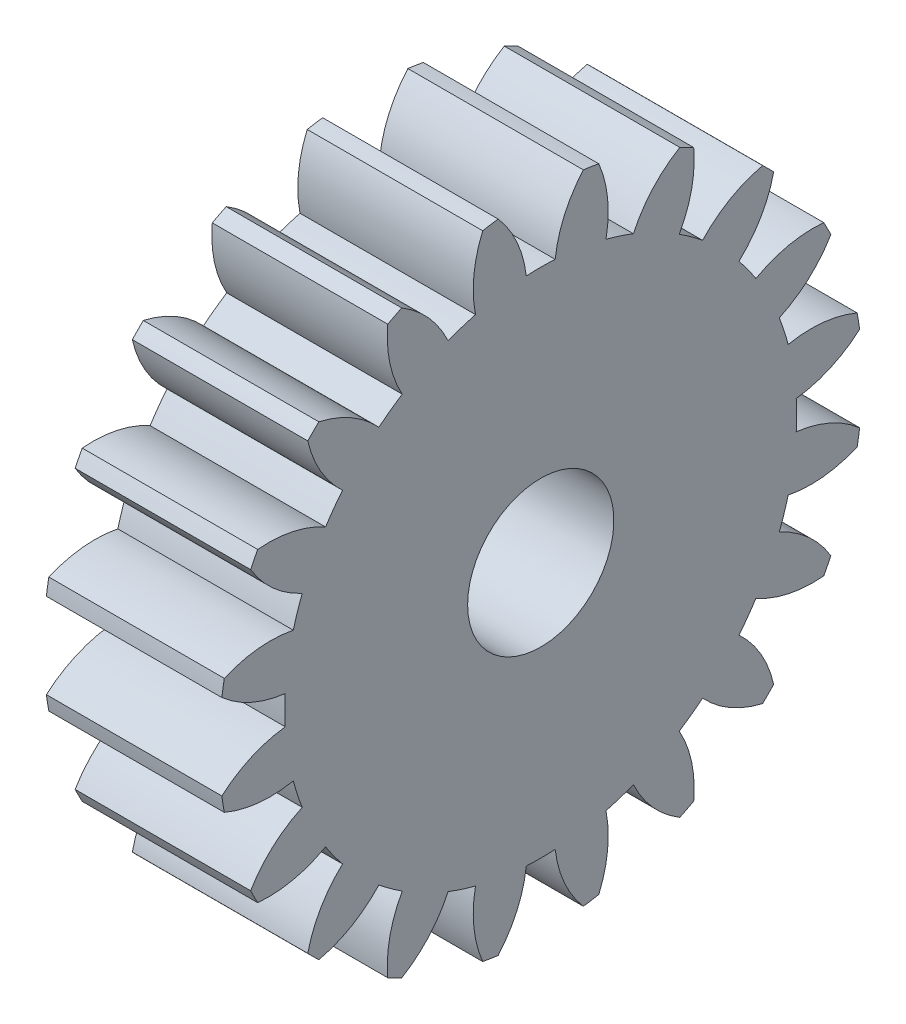
SolidWorks part; units mm, degrees
ref_plane "Plane1" through (0, 0, 0) normal (0, 0, 1) x (1, 0, 0)
ref_plane "Plane2" through (0, 0, 0) normal (0, 1, 0) x (1, 0, 0)
ref_plane "Plane3" through (0, 0, 0) normal (1, 0, 0) x (0, 0, -1)
sketch "HoldingSke" plane through (0, 0, 0) normal (0, 1, 0) x (1, 0, 0)
  line L0 (0, 0) -> (0.4698, -0.171)
  line L1 (-15, 0) -> (100, 0) construction
  line L2 (0, 0) -> (-2.1039, 2.3779)
  line L3 (0, 0) -> (-11.863, 4.5341)
  line L4 (0, 0) -> (8.1152, 2.9537)
  line L5 (0, 0) -> (-46.8476, -17.4728)
  line L6 (0, 0) -> (-9.9476, -6.7116)
  line L7 (-2.1039, 2.3779) -> (8.6586, 51.2059)
  line L8 (-76.2, 54.61) -> (-74.4, 54.61)
  line L9 (-71.009, 38.7566) -> (-53.1078, 45.2721)
  line L10 (-76.2, 71.12) -> (104.1128, 71.12)
  line L11 (0, 0) -> (-12, 0)
  line L12 (-76.2, 101.6) -> (-76.133, 101.6)
  line L13 (24.9733, 27.94) -> (52.9518, 28.4284)
  line L14 (24.9733, 27.94) -> (24.9743, 27.94)
  line L15 (24.9733, 27.94) -> (100.4006, 29.5858)
  line L16 (-63.627, -2) -> (-12.827, -2)
  circle A0 centre (0, 0) radius 5
  circle A1 centre (0, 0) radius 17.499
  circle A2 centre (0, 0) radius 37.5
  circle A3 centre (0, 0) radius 5
  dimension "MHD" = 34.998
  dimension "Hub_dia" = 75
  dimension "Bore" = 10
  dimension "MBD" = 10
  dimension "Num_teeth" = 20
  dimension "Pitch" = 0.5
  dimension "Overall_len" = 50
  dimension "Show_teeth" = 20
  dimension "Thickness" = 12
  dimension "OAL" = 50.0001
  dimension "T_dim" = 1.8
  dimension "Ap" = 20
  dimension "H" = 19.05
  dimension "Pitch_radius" = 180.3128
  dimension "Width" = 12
  dimension "Backlash" = 0.067
  dimension "Addendum_fac" = 1
  dimension "Dedendum_fac" = 1.25
  dimension "Clearance_fac" = 0.25
  dimension "Dedendum_add" = 0.001
  dimension "Module" = 2
sketch "BasProSke" plane through (0, 0, 0) normal (0, 1, 0) x (1, 0, 0)
  line L0 (-10, 0) -> (60, 0) construction
  line L1 (0, 0) -> (0, 22)
  line L2 (0, 0) -> (12, 0)
  line L3 (12, 0) -> (12, 22)
  line L4 (12, 22) -> (0, 22)
  dimension "Thickness" = 12
  dimension "Diameter" = 44
revolve "Base-Revolve" add sketch "BasProSke" angle 360 about L0
sketch "TooCutSke" plane through (0, 0, 0) normal (1, 0, 0) x (0, 0, -1)
  line L1 (0, 0) -> (0, 107) construction
  line L2 (0, 0) -> (-1.6864, 19.9288) construction
  line L3 (0, 0) -> (-6.2409, 39.4033) construction
  line L4 (-1.6864, 19.9288) -> (-3.1204, 19.7016) construction
  arc A0 (0.9862, 17.4712) -> (-0.9862, 17.4712) centre (0, 0) ccw
  arc A1 (2.9329, 21.8293) -> (-2.9329, 21.8293) centre (0, 0) ccw
  circle A2 centre (0, 0) radius 20 construction
  circle A3 centre (0, 0) radius 18.7939 construction
  arc A4 (-0.9862, 17.4712) -> (-2.9329, 21.8293) centre (-8.9313, 16.536) ccw
  arc A5 (2.9329, 21.8293) -> (0.9862, 17.4712) centre (8.9313, 16.536) ccw
  dimension "Root_dia" = 34.998
  dimension "Overcut_dia" = 44.0508
  dimension "Pitch_dia" = 40
  dimension "Base_dia" = 37.5877
  dimension "Flank_rad" = 8
  dimension "Half_ang" = 9
  dimension "Half_CT" = 1.4519
extrude "ToothCut" cut sketch "TooCutSke" along normal through all
fillet "Breaks" [suppressed] radius 0.04
fillet "RootFillets" [suppressed] radius 0.501
pattern_circular "TeethCuts" count 20 every 18 about axis through (-10, 0, 0) along (1, 0, 0) of "ToothCut", "RootFillets", "Breaks"
sketch "HubNeaOneSke" plane through (0, 0, 0) normal (-1, 0, 0) x (0, 0, 1)
  circle A0 centre (0, 0) radius 17.499
  dimension "Diameter" = 34.998
extrude "HubNearOne" [suppressed] add sketch "HubNeaOneSke" along normal blind 38.0001
sketch "HubNeaBotSke" plane through (0, 0, 0) normal (-1, 0, 0) x (0, 0, 1)
  circle A0 centre (0, 0) radius 17.499
  dimension "Diameter" = 34.998
extrude "HubNearBoth" [suppressed] add sketch "HubNeaBotSke" along normal blind 19
ref_plane "FarPln" through (12, 0, 0) normal (1, 0, 0) x (0, 0, -1)
sketch "HubFarSke" plane through (12, 0, 0) normal (1, 0, 0) x (0, 0, -1)
  circle A0 centre (0, 0) radius 17.499
  dimension "Diameter" = 34.998
extrude "HubFar" [suppressed] add sketch "HubFarSke" along normal blind 19
sketch "BorSke" plane through (0, 0, 0) normal (1, 0, 0) x (0, 0, -1)
  circle A0 centre (0, 0) radius 5
  dimension "Diameter" = 10
extrude "Bore" cut sketch "BorSke" along normal mid plane 100.0001
sketch "KeySke" plane through (0, 0, 0) normal (1, 0, 0) x (0, 0, -1)
  line L0 (-2, 0) -> (-2, 6.8)
  line L1 (-2, 6.8) -> (2, 6.8)
  line L2 (2, 6.8) -> (2, 0)
  line L3 (0, 0) -> (0, 34) construction
  line L4 (-2, 0) -> (2, 0)
  dimension "Offset" = 6.8
  dimension "Width" = 4
extrude "Keyway" [suppressed] cut sketch "KeySke" along normal mid plane 100.0001
pattern_circular "Keyway2" [suppressed] count 2 every 90 about axis through (-10, 0, 0) along (1, 0, 0)
equation "' \"Module@HoldingSke\" = 6.35"
equation "' \"Num_teeth@HoldingSke\" = 12"
equation "' \"Ap@HoldingSke\" =  20"
equation "' \"Ap@HoldingSke\" = 20"
equation "' \"Width@HoldingSke\" = 0.5 * 25.4"
equation "' \"Hub_dia@HoldingSke\"= 1 * 25.4"
equation "' \"Hub_dia@HoldingSke\" = 1 * 25.4"
equation "' \"Overall_len@HoldingSke\" = 1.0 * 25.4"
equation "' \"Bore@HoldingSke\" = 0.75 * 25.4"
equation "' \"T_dim@HoldingSke\" = 0.1 * 25.4"
equation "' \"Width@KeySke\" = 0.25 * 25.4"
equation "' \"Show_teeth@HoldingSke\" = 13"
equation "' \"Backlash@HoldingSke\" = 0.009 * 25.4"
equation "' \"Addendum_fac@HoldingSke\" = 1.0"
equation "' \"Dedendum_fac@HoldingSke\" = 1.25"
equation "' \"Dedendum_add@HoldingSke\" = 0.00005 * 25.4"
equation "' \"Clearance_fac@HoldingSke\" = 0.25"
equation "\"Pitch@HoldingSke\" = 1 / \"Module@HoldingSke\""
equation "\"Overcut_dia@TooCutSke\" = (\"Num_teeth@HoldingSke\" + 2 * \"Addendum_fac@HoldingSke\") / \"Pitch@HoldingSke\" + 0.002 * 25.4"
equation "\"Pitch_dia@TooCutSke\" = \"Num_teeth@HoldingSke\" / \"Pitch@HoldingSke\""
equation "\"Base_dia@TooCutSke\" = \"Num_teeth@HoldingSke\" / \"Pitch@HoldingSke\" * cos((\"Ap@HoldingSke\"  * 3.14159265 / 180))"
equation "\"Root_dia@TooCutSke\" = (\"Num_teeth@HoldingSke\" + 2) / \"Pitch@HoldingSke\" - 2 * (\"Addendum_fac@HoldingSke\" + \"Dedendum_fac@HoldingSke\") / \"Pitch@HoldingSke\" - \"Dedendum_add@HoldingSke\" * 2"
equation "\"Half_ang@TooCutSke\" = 180 / \"Num_teeth@HoldingSke\""
equation "\"Half_CT@TooCutSke\" = \"Num_teeth@HoldingSke\" / \"Pitch@HoldingSke\" * sin((3.14159265 / 2 / \"Num_teeth@HoldingSke\")) / 2 - 7 * \"Backlash@HoldingSke\" / 4"
equation "\"Flank_rad@TooCutSke\" = \"Num_teeth@HoldingSke\" / \"Pitch@HoldingSke\" / 5"
equation "\"Radius@RootFillets\" = \"Clearance_fac@HoldingSke\" / \"Pitch@HoldingSke\" + \"Dedendum_add@HoldingSke\""
equation "\"Break_rad@Breaks\" = 0.02 / \"Pitch@HoldingSke\""
equation "\"Thickness@HoldingSke\" = \"Width@HoldingSke\""
equation "\"OAL@HoldingSke\" = \"Thickness@HoldingSke\""
equation "\"MHD@HoldingSke\" = (\"Num_teeth@HoldingSke\" + 2) / \"Pitch@HoldingSke\" - 2 * (\"Addendum_fac@HoldingSke\" + \"Dedendum_fac@HoldingSke\")  / \"Pitch@HoldingSke\" - \"Dedendum_add@HoldingSke\" * 2"
equation "\"MBD@HoldingSke\" = (\"Num_teeth@HoldingSke\" + 2) / \"Pitch@HoldingSke\" - 2 * (\"Addendum_fac@HoldingSke\" + \"Dedendum_fac@HoldingSke\")  / \"Pitch@HoldingSke\" - \"Dedendum_add@HoldingSke\" * 2 - 0.002 * 25.4"
equation "\"MHD@HoldingSke\" = ((sgn( \"MHD@HoldingSke\" - \"Hub_dia@HoldingSke\" )-1)*( \"MHD@HoldingSke\" - \"Hub_dia@HoldingSke\" ))/-2+ \"Hub_dia@HoldingSke\""
equation "\"MBD@HoldingSke\" = ((sgn( \"MBD@HoldingSke\" - \"Bore@HoldingSke\" )-1)*( \"MBD@HoldingSke\" - \"Bore@HoldingSke\" ))/-2+ \"Bore@HoldingSke\""
equation "\"OAL@HoldingSke\" = ((sgn( \"OAL@HoldingSke\" - \"Overall_len@HoldingSke\" )+1)*( \"OAL@HoldingSke\" - \"Overall_len@HoldingSke\" ))/2 + \"Overall_len@HoldingSke\" + 0.000002 * 25.4"
equation "\"Num_teeth@TeethCuts\" = int( \"Show_teeth@HoldingSke\" ) + 1"
equation "\"Num_teeth@TeethCuts\" = ((sgn( \"Num_teeth@TeethCuts\" - \"Num_teeth@HoldingSke\" )-1)*( \"Num_teeth@TeethCuts\" - \"Num_teeth@HoldingSke\" ))/-2+ \"Num_teeth@HoldingSke\""
equation "\"Num_teeth@TeethCuts\" = ((sgn( \"Num_teeth@TeethCuts\" - 2.0)+1)*( \"Num_teeth@TeethCuts\" - 2.0))/2 +2.0"
equation "\"Angle@TeethCuts\" = 360.0 / \"Num_teeth@HoldingSke\""
equation "\"Diameter@BasProSke\" = (\"Num_teeth@HoldingSke\" + 2 * \"Addendum_fac@HoldingSke\") / \"Pitch@HoldingSke\""
equation "\"Thickness@BasProSke\"  = \"Thickness@HoldingSke\""
equation "' \"Fillet_rad@BasProSke\" =  \"Thickness@HoldingSke\" * 0.05"
equation "' \"Fillet_rad@BasProSke\" = \"Thickness@HoldingSke\" * 0.05"
equation "\"MHD@HoldingSke\" = ((sgn( \"MHD@HoldingSke\" - \"Root_dia@TooCutSke\" )-1)*( \"MHD@HoldingSke\" - \"Root_dia@TooCutSke\" ))/-2+ \"Root_dia@TooCutSke\""
equation "\"Diameter@HubNeaOneSke\" = \"MHD@HoldingSke\""
equation "\"Length@HubNearOne\" = \"OAL@HoldingSke\" - \"Thickness@BasProSke\""
equation "\"Diameter@HubNeaBotSke\" = \"MHD@HoldingSke\""
equation "\"Length@HubNearBoth\" = ( \"OAL@HoldingSke\" - \"Thickness@BasProSke\" ) / 2.0"
equation "\"Thickness@FarPln\" = \"Thickness@BasProSke\""
equation "\"Diameter@HubFarSke\" = \"MHD@HoldingSke\""
equation "\"Length@HubFar\" = ( \"OAL@HoldingSke\" - \"Thickness@BasProSke\" ) / 2.0"
equation "\"Diameter@BorSke\" = \"MBD@HoldingSke\""
equation "\"D1@Bore\" = \"OAL@HoldingSke\" * 2.0"
equation "\"D1@Keyway\" = \"OAL@HoldingSke\" * 2.0"
equation "\"Offset@KeySke\" = \"T_dim@HoldingSke\" + \"MBD@HoldingSke\" / 2.0"
